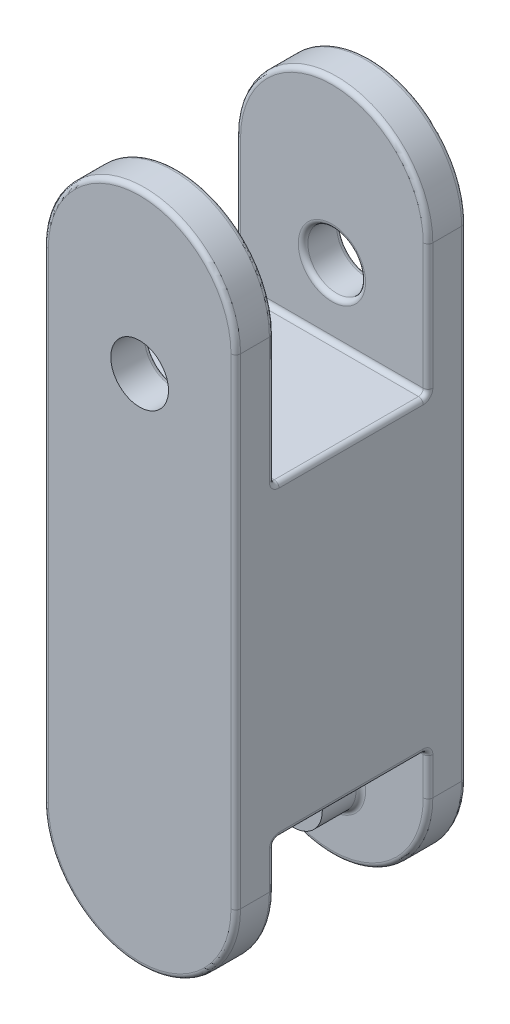
SolidWorks part; units mm, degrees
material "AISI 316 Stainless Steel Sheet (SS)"
ref_plane "Front Plane" through (0, 0, 0) normal (0, 0, 1) x (1, 0, 0)
ref_plane "Top Plane" through (0, 0, 0) normal (0, 1, 0) x (1, 0, 0)
ref_plane "Right Plane" through (0, 0, 0) normal (1, 0, 0) x (0, 0, -1)
sketch "Sketch1" plane through (0, 0, 0) normal (0, 0, 1) x (1, 0, 0)
  line L0 (0, -317.5) -> (0, 317.5) construction
  line L1 (-127, -317.5) -> (-127, 317.5)
  line L2 (127, -317.5) -> (127, 317.5)
  arc A0 (-127, -317.5) -> (127, -317.5) centre (0, -317.5) ccw
  arc A1 (127, 317.5) -> (-127, 317.5) centre (0, 317.5) ccw
  point P2 (0, 0)
  dimension "D2" = 127
  dimension "D1" = 635
extrude "Boss-Extrude1" add sketch "Sketch1" along normal blind 50.8 contours L2 A1 L1 A0
sketch "Sketch3" plane through (0, 0, 50.8) normal (0, 0, 1) x (1, 0, 0)
  circle A0 centre (0, 234.3225) radius 38.1
  dimension "D1" = 76.2
extrude "Cut-Extrude1" cut sketch "Sketch3" against normal blind 101.6
sketch "Sketch6" plane through (0, 0, 50.8) normal (0, 0, 1) x (1, 0, 0)
  line L0 (-127, -317.5) -> (-127, 317.5) construction
  line L1 (-127, -261.5631) -> (127, -261.5631)
  line L2 (-127, -261.5631) -> (-127, 144.8369)
  line L3 (-127, 144.8369) -> (127, 144.8369)
  line L4 (127, -261.5631) -> (127, 144.8369)
  line L5 (127, -317.5) -> (127, 317.5) construction
  dimension "D1" = 406.4
extrude "Boss-Extrude5" add sketch "Sketch6" along normal blind 101.6
sketch "Sketch7" plane through (0, 0, 50.8) normal (0, 0, 1) x (1, 0, 0)
  circle A0 centre (0, -348.22) radius 38.1
  dimension "D1" = 76.2
extrude "Boss-Extrude6" add sketch "Sketch7" along normal blind 50.8
mirror "Mirror3" about plane through (0, 0, 152.4) normal (0, 0, -1) of bodies 109
fillet "Fillet1" radius 6.35 4 edges at (127, 0, 304.8) (-127, 0, 304.8) (0, 444.5, 304.8) (0, -444.5, 304.8)
fillet "Fillet2" radius 6.35 5 edges at (127, 0, 0) (0, 444.5, 0) (-127, 0, 0) (0, -444.5, 0) (38.1, 234.3225, 0)
fillet "Fillet3" radius 6.35 24 edges at (127, -261.5631, 152.4) (-127, -261.5631, 152.4) (127, 144.8369, 152.4) (-127, 144.8369, 152.4) (127, -289.5315, 254) (-127, -289.5315, 254) (0, -444.5, 254) (0, -261.5631, 254) (38.1, -348.22, 254) (127, -289.5315, 50.8) (0, -444.5, 50.8) (-127, -289.5315, 50.8) (0, -261.5631, 50.8) (38.1, -348.22, 50.8) (38.1, 234.3225, 50.8) (-127, 231.1685, 50.8) (0, 444.5, 50.8) (127, 231.1685, 50.8) (0, 144.8369, 50.8) (38.1, 234.3225, 254) (-127, 231.1685, 254) (127, 231.1685, 254) (0, 444.5, 254) (0, 144.8369, 254)
